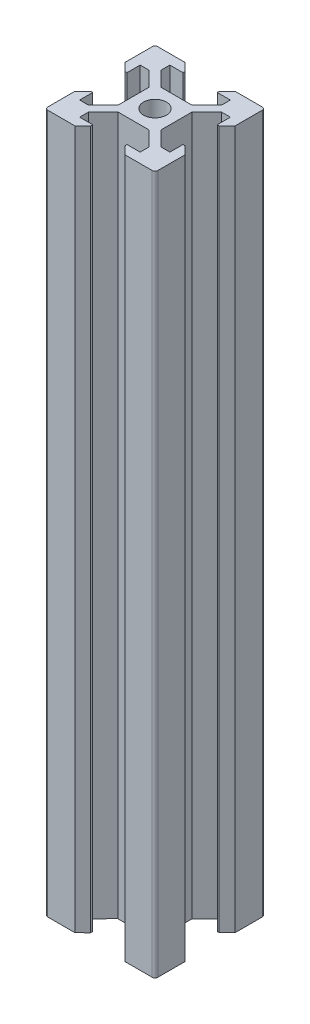
SolidWorks part; units mm, degrees
ref_plane "Front Plane" through (0, 0, 0) normal (0, 0, 1) x (1, 0, 0)
ref_plane "Top Plane" through (0, 0, 0) normal (0, 1, 0) x (1, 0, 0)
ref_plane "Right Plane" through (0, 0, 0) normal (1, 0, 0) x (0, 0, -1)
sketch "Sketch1" plane through (0, 0, 0) normal (1, 0, 0) x (0, 0, -1)
  line L0 (0, 0) -> (0, 127)
  dimension "D1" = 127
other "Vslot2020 2020(5)"
ref_plane "Plane5" through (0, 0, 0) normal (0, 1, 0) x (0, 0, 1)
sketch "Sketch2" plane through (0, 0, 0) normal (0, 1, 0) x (0, 0, 1)
  line L58 (13.9, 7.1491) -> (13.9, 12.8445)
  line L59 (13.9, 12.8445) -> (16.5585, 15.4922)
  line L60 (16.5585, 15.4922) -> (16.5507, 15.5)
  line L61 (16.5507, 15.5) -> (18.2, 15.5)
  line L62 (18.2, 15.5) -> (18.2, 13.12)
  line L63 (18.2, 13.12) -> (18.5344, 13.12)
  line L64 (18.5344, 13.12) -> (20, 14.58)
  line L65 (20, 14.58) -> (20, 19.5)
  line L66 (19.5, 20) -> (14.575, 20)
  line L67 (14.575, 20) -> (13.12, 18.545)
  line L68 (13.12, 18.545) -> (13.12, 18.2)
  line L69 (13.12, 18.2) -> (15.5, 18.2)
  line L70 (15.5, 18.2) -> (15.5, 16.555)
  line L71 (15.5, 16.555) -> (12.8341, 13.9)
  line L72 (12.8341, 13.9) -> (7.155, 13.9)
  line L73 (7.155, 13.9) -> (4.5, 16.555)
  line L74 (4.5, 16.555) -> (4.5, 18.2)
  line L75 (4.5, 18.2) -> (6.875, 18.2)
  line L76 (6.875, 18.2) -> (6.875, 18.545)
  line L77 (6.875, 18.545) -> (5.42, 20)
  line L78 (5.42, 20) -> (0.5, 20)
  line L79 (0, 19.5) -> (0, 14.58)
  line L80 (0, 14.58) -> (1.46, 13.12)
  line L81 (1.46, 13.12) -> (1.8, 13.12)
  line L82 (1.8, 13.12) -> (1.8, 15.5)
  line L83 (1.8, 15.5) -> (3.445, 15.5)
  line L84 (3.445, 15.5) -> (3.4393, 15.4943)
  line L85 (3.4393, 15.4943) -> (6.0943, 12.8393)
  line L86 (6.0943, 12.8393) -> (6.1, 12.845)
  line L87 (6.1, 12.845) -> (6.1, 7.1491)
  line L88 (6.1, 7.1491) -> (3.4393, 4.5)
  line L89 (3.4393, 4.5) -> (1.8, 4.5)
  line L90 (1.8, 4.5) -> (1.8, 6.88)
  line L91 (1.8, 6.88) -> (1.46, 6.88)
  line L92 (1.46, 6.88) -> (0, 5.42)
  line L93 (0, 5.42) -> (0, 0.5)
  line L94 (0.5, 0) -> (5.42, 0)
  line L95 (5.42, 0) -> (6.875, 1.455)
  line L96 (6.875, 1.455) -> (6.875, 1.8)
  line L97 (6.875, 1.8) -> (4.5, 1.8)
  line L98 (4.5, 1.8) -> (4.5, 3.4393)
  line L99 (4.5, 3.4393) -> (7.1583, 6.0861)
  line L100 (7.1583, 6.0861) -> (7.1445, 6.1)
  line L101 (7.1445, 6.1) -> (12.8546, 6.1)
  line L102 (12.8546, 6.1) -> (12.8412, 6.0865)
  line L103 (12.8412, 6.0865) -> (15.4997, 3.4375)
  line L104 (15.4997, 3.4375) -> (15.5, 3.4377)
  line L105 (15.5, 3.4377) -> (15.5, 1.8)
  line L106 (15.5, 1.8) -> (13.12, 1.8)
  line L107 (13.12, 1.8) -> (13.12, 1.455)
  line L108 (13.12, 1.455) -> (14.575, 0)
  line L109 (14.575, 0) -> (19.5, 0)
  line L110 (20, 0.5) -> (20, 5.42)
  line L111 (20, 5.42) -> (18.6069, 6.88)
  line L112 (18.6069, 6.88) -> (18.2, 6.88)
  line L113 (18.2, 6.88) -> (18.2, 4.5)
  line L114 (18.2, 4.5) -> (16.5585, 4.5)
  line L115 (16.5585, 4.5) -> (13.9, 7.1491)
  line L116 (13.9, 7.1491) -> (13.9, 12.8445)
  line L117 (13.9, 12.8445) -> (16.5585, 15.4922)
  line L118 (16.5585, 15.4922) -> (16.5507, 15.5)
  line L119 (16.5507, 15.5) -> (18.2, 15.5)
  line L120 (18.2, 15.5) -> (18.2, 13.12)
  line L121 (18.2, 13.12) -> (18.5344, 13.12)
  line L122 (18.5344, 13.12) -> (20, 14.58)
  line L123 (20, 14.58) -> (20, 19.5)
  line L124 (19.5, 20) -> (14.575, 20)
  line L125 (14.575, 20) -> (13.12, 18.545)
  line L126 (13.12, 18.545) -> (13.12, 18.2)
  line L127 (13.12, 18.2) -> (15.5, 18.2)
  line L128 (15.5, 18.2) -> (15.5, 16.555)
  line L129 (15.5, 16.555) -> (12.8341, 13.9)
  line L130 (12.8341, 13.9) -> (7.155, 13.9)
  line L131 (7.155, 13.9) -> (4.5, 16.555)
  line L132 (4.5, 16.555) -> (4.5, 18.2)
  line L133 (4.5, 18.2) -> (6.875, 18.2)
  line L134 (6.875, 18.2) -> (6.875, 18.545)
  line L135 (6.875, 18.545) -> (5.42, 20)
  line L136 (5.42, 20) -> (0.5, 20)
  line L137 (0, 19.5) -> (0, 14.58)
  line L138 (0, 14.58) -> (1.46, 13.12)
  line L139 (1.46, 13.12) -> (1.8, 13.12)
  line L140 (1.8, 13.12) -> (1.8, 15.5)
  line L141 (1.8, 15.5) -> (3.445, 15.5)
  line L142 (3.445, 15.5) -> (3.4393, 15.4943)
  line L143 (3.4393, 15.4943) -> (6.0943, 12.8393)
  line L144 (6.0943, 12.8393) -> (6.1, 12.845)
  line L145 (6.1, 12.845) -> (6.1, 7.1491)
  line L146 (6.1, 7.1491) -> (3.4393, 4.5)
  line L147 (3.4393, 4.5) -> (1.8, 4.5)
  line L148 (1.8, 4.5) -> (1.8, 6.88)
  line L149 (1.8, 6.88) -> (1.46, 6.88)
  line L150 (1.46, 6.88) -> (0, 5.42)
  line L151 (0, 5.42) -> (0, 0.5)
  line L152 (0.5, 0) -> (5.42, 0)
  line L153 (5.42, 0) -> (6.875, 1.455)
  line L154 (6.875, 1.455) -> (6.875, 1.8)
  line L155 (6.875, 1.8) -> (4.5, 1.8)
  line L156 (4.5, 1.8) -> (4.5, 3.4393)
  line L157 (4.5, 3.4393) -> (7.1583, 6.0861)
  line L158 (7.1583, 6.0861) -> (7.1445, 6.1)
  line L159 (7.1445, 6.1) -> (12.8546, 6.1)
  line L160 (12.8546, 6.1) -> (12.8412, 6.0865)
  line L161 (12.8412, 6.0865) -> (15.4997, 3.4375)
  line L162 (15.4997, 3.4375) -> (15.5, 3.4377)
  line L163 (15.5, 3.4377) -> (15.5, 1.8)
  line L164 (15.5, 1.8) -> (13.12, 1.8)
  line L165 (13.12, 1.8) -> (13.12, 1.455)
  line L166 (13.12, 1.455) -> (14.575, 0)
  line L167 (14.575, 0) -> (19.5, 0)
  line L168 (20, 0.5) -> (20, 5.42)
  line L169 (20, 5.42) -> (18.6069, 6.88)
  line L170 (18.6069, 6.88) -> (18.2, 6.88)
  line L171 (18.2, 6.88) -> (18.2, 4.5)
  line L172 (18.2, 4.5) -> (16.5585, 4.5)
  line L173 (16.5585, 4.5) -> (13.9, 7.1491)
  circle A0 centre (10, 10) radius 2.0746 construction
  circle A1 centre (10, 10) radius 2.0746
  arc A4 (20, 19.5) -> (19.5, 20) centre (19.5, 19.5) ccw
  arc A5 (0.5, 20) -> (0, 19.5) centre (0.5, 19.5) ccw
  arc A6 (0, 0.5) -> (0.5, 0) centre (0.5, 0.5) ccw
  arc A7 (19.5, 0) -> (20, 0.5) centre (19.5, 0.5) ccw
  arc A8 (20, 19.5) -> (19.5, 20) centre (19.5, 19.5) ccw
  arc A9 (0.5, 20) -> (0, 19.5) centre (0.5, 19.5) ccw
  arc A10 (0, 0.5) -> (0.5, 0) centre (0.5, 0.5) ccw
  arc A11 (19.5, 0) -> (20, 0.5) centre (19.5, 0.5) ccw
  point P16 (0, 0)
  dimension "D1" = 0
ref_plane "Plane6" through (0, 0, 9.9946) normal (0, 0, 1) x (1, 0, 0)
ref_plane "Plane7" through (9.997, 0, 0) normal (1, 0, 0) x (0, 0, -1)
ref_plane "Plane8" through (0, 63.5, 0) normal (0, 1, 0) x (1, 0, 0)
